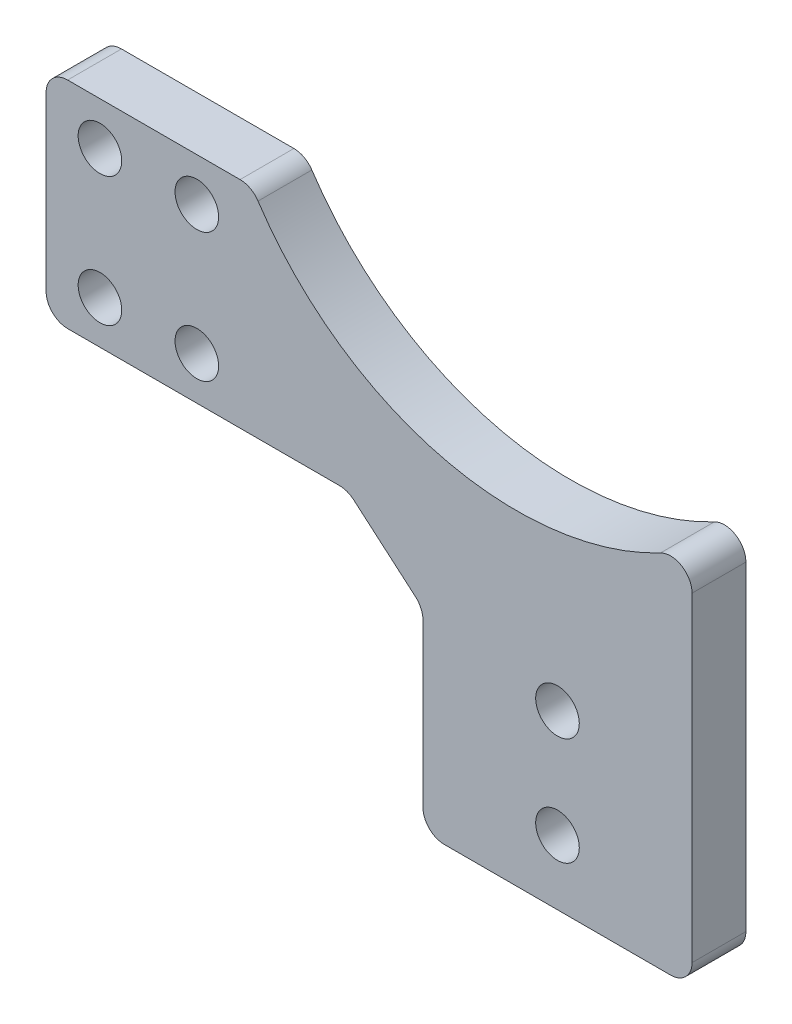
SolidWorks part; units mm, degrees
material "ABS"
ref_plane "前视基准面" through (0, 0, 0) normal (0, 0, 1) x (1, 0, 0)
ref_plane "上视基准面" through (0, 0, 0) normal (0, 1, 0) x (1, 0, 0)
ref_plane "右视基准面" through (0, 0, 0) normal (1, 0, 0) x (0, 0, -1)
other "Configuration Table"
sketch "草图1" plane through (0, 0, 0) normal (0, 0, 1) x (1, 0, 0)
  line L0 (0, 0) -> (0, -24)
  line L1 (0, -24) -> (25, -24)
  line L2 (25, -24) -> (25, 17.2566)
  line L3 (-15.8854, 26) -> (-35, 26)
  line L4 (-35, 26) -> (-35, 6)
  line L5 (-35, 6) -> (-7, 6)
  line L6 (-7, 6) -> (0, 0)
  arc A0 (25, 17.2566) -> (-15.8854, 26) centre (8.7, 41) cw
  dimension "D3" = 28.8
  dimension "D1" = 6
  dimension "D2" = 7
  dimension "D4" = 25
  dimension "D5" = 20
  dimension "D6" = 16.3
  dimension "D7" = 35
  dimension "D8" = 60
  dimension "D9" = 50
extrude "凸台-拉伸1" add sketch "草图1" along normal mid plane 5
fillet "圆角1" radius 2 6 edges at (-7, 6, 0) (-35, 6, 0) (25, -24, 0) (0, -24, 0) (0, 0, 0) (-35, 26, 0)
fillet "圆角2" radius 2 2 edges at (25, 17.2566, 0) (-15.8854, 26, 0)
sketch "草图2" plane through (0, 0, 2.5) normal (0, 0, 1) x (1, 0, 0)
  line L0 (-33, 6) -> (-7.7398, 6) construction
  line L1 (7.5, -12) -> (17.5, -12) construction
  line L2 (7.5, -12) -> (7.5, -2) construction
  line L3 (7.5, -2) -> (17.5, -2) construction
  line L4 (17.5, -12) -> (17.5, -2) construction
  line L5 (7.5, -12) -> (17.5, -2) construction
  line L6 (7.5, -2) -> (17.5, -12) construction
  line L7 (12.5, -7) -> (12.5, -24) construction
  line L8 (2, -24) -> (23, -24) construction
  circle A4 centre (12.5, -2) radius 2.025
  circle A5 centre (12.5, -12) radius 2.025
  point P0 (12.5, -7)
  dimension "D4" = 4.05
  dimension "D1" = 8
  dimension "D2" = 10
  dimension "D3" = 10
extrude "切除-拉伸1" cut sketch "草图2" against normal through all
sketch "草图3" plane through (0, 0, 2.5) normal (0, 0, 1) x (1, 0, 0)
  line L0 (0, -0.9199) -> (0, -22) construction
  line L1 (0, -18) -> (25, -18)
  line L2 (0, -18) -> (0, -24)
  line L3 (0, -24) -> (25, -24)
  line L4 (25, -18) -> (25, -24)
  line L5 (2, -24) -> (23, -24) construction
  line L6 (25, -22) -> (25, 13.7209) construction
  dimension "D1" = 6
extrude "切除-拉伸2" cut sketch "草图3" against normal through all
fillet "圆角3" radius 2 2 edges at (25, -18, 0) (0, -18, 0)
sketch "草图4" plane through (0, 0, 2.5) normal (0, 0, 1) x (1, 0, 0)
  line L0 (-35, 24) -> (-35, 8) construction
  line L1 (-16.9835, 26) -> (-33, 26) construction
  line L2 (-33, 6) -> (-7.7398, 6) construction
  circle A0 centre (-30, 22) radius 2.025
  circle A1 centre (-30, 10) radius 2.025
  dimension "D1" = 4.05
  dimension "D3" = 5
  dimension "D4" = 4
  dimension "D5" = 4
  dimension "D2" = 5
extrude "切除-拉伸3" cut sketch "草图4" against normal through all both and the other way through all
sketch "草图5" plane through (0, 0, 2.5) normal (0, 0, 1) x (1, 0, 0)
  line L1 (-30, 22) -> (-21, 22) construction
  line L2 (-30, 22) -> (-30, 10) construction
  line L3 (-30, 10) -> (-21, 10) construction
  line L4 (-21, 22) -> (-21, 10) construction
  circle A0 centre (-30, 10) radius 2.025 construction
  circle A1 centre (-21, 10) radius 2.025
  circle A2 centre (-21, 22) radius 2.025
  dimension "D2" = 4.05
  dimension "D1" = 9
extrude "切除-拉伸4" cut sketch "草图5" against normal through all both
